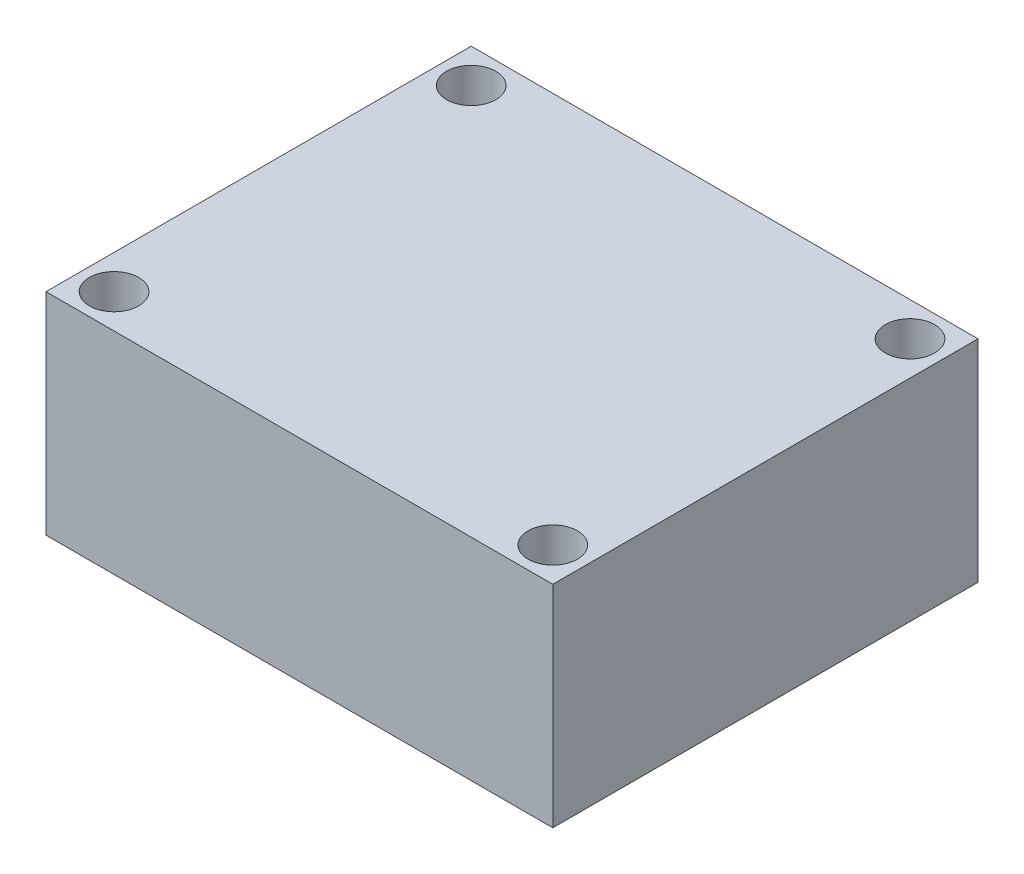
SolidWorks part; units mm, degrees
ref_plane "Front Plane" through (0, 0, 0) normal (0, 0, 1) x (1, 0, 0)
ref_plane "Top Plane" through (0, 0, 0) normal (0, 1, 0) x (1, 0, 0)
ref_plane "Right Plane" through (0, 0, 0) normal (1, 0, 0) x (0, 0, -1)
sketch "Sketch1" plane through (0, 0, 0) normal (0, 1, 0) x (1, 0, 0)
  line L1 (-18.923, -15.875) -> (18.923, -15.875)
  line L2 (-18.923, -15.875) -> (-18.923, 15.875)
  line L3 (-18.923, 15.875) -> (18.923, 15.875)
  line L4 (18.923, -15.875) -> (18.923, 15.875)
  line L5 (-18.923, -15.875) -> (18.923, 15.875) construction
  line L6 (-18.923, 15.875) -> (18.923, -15.875) construction
  point P0 (0, 0)
  dimension "D1" = 37.846
  dimension "D2" = 31.75
extrude "Boss-Extrude1" add sketch "Sketch1" along normal mid plane 15.748
sketch "Sketch2" plane through (0, -7.874, 0) normal (0, -1, 0) x (1, 0, 0)
  line L0 (-18.923, 15.875) -> (18.923, 15.875) construction
  line L1 (-18.923, -15.875) -> (-18.923, 15.875) construction
  line L2 (0, 0) -> (0, 15.875) construction
  line L3 (0, 15.875) -> (0, -15.875) construction
  line L4 (18.923, -15.875) -> (-18.923, -15.875) construction
  line L5 (0, 0) -> (18.923, 0) construction
  line L6 (18.923, 15.875) -> (18.923, -15.875) construction
  line L7 (18.923, 0) -> (-18.923, 0) construction
  circle A0 centre (-16.383, 13.335) radius 1.8415
  circle A1 centre (16.383, 13.335) radius 1.8415
  circle A2 centre (16.383, -13.335) radius 1.8415
  circle A3 centre (-16.383, -13.335) radius 1.8415
  dimension "D1" = 3.683
  dimension "D2" = 2.54
  dimension "D3" = 2.54
extrude "Cut-Extrude1" cut sketch "Sketch2" against normal through all
